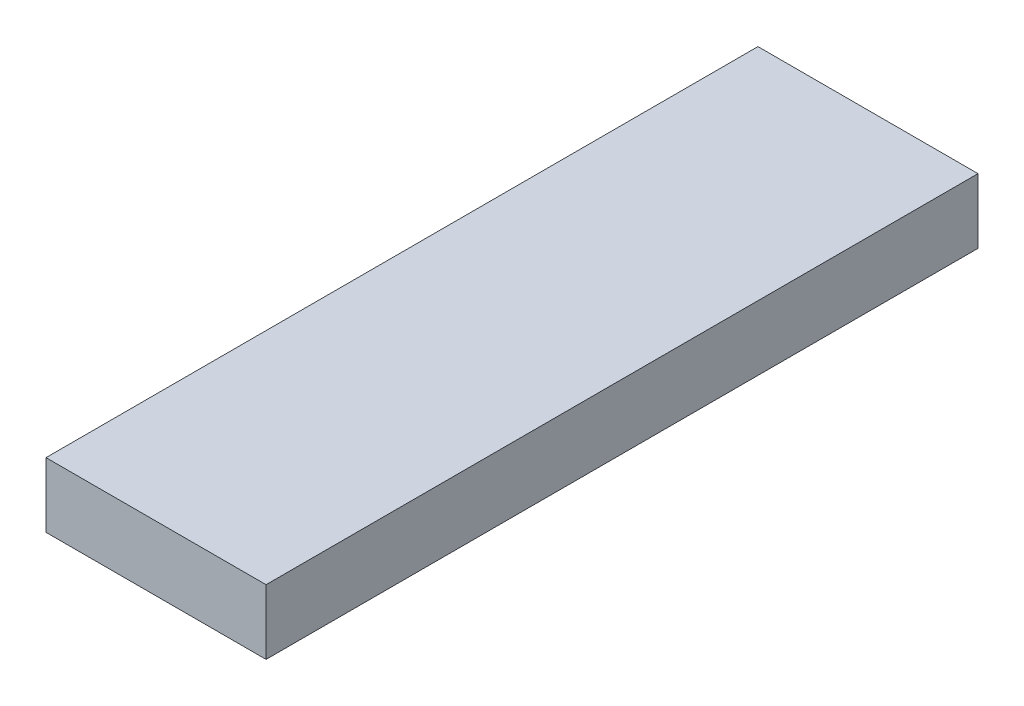
SolidWorks part; units mm, degrees
ref_plane "Front Plane" through (0, 0, 0) normal (0, 0, 1) x (1, 0, 0)
ref_plane "Top Plane" through (0, 0, 0) normal (0, 1, 0) x (1, 0, 0)
ref_plane "Right Plane" through (0, 0, 0) normal (1, 0, 0) x (0, 0, -1)
sketch "Sketch2" plane through (0, 0, 0) normal (0, 1, 0) x (1, 0, 0)
  line L1 (-4.6, 4.4326) -> (29.4, 4.4326)
  line L2 (-4.6, 4.4326) -> (-4.6, -50.5674)
  line L3 (-4.6, -50.5674) -> (29.4, -50.5674)
  line L4 (29.4, 4.4326) -> (29.4, -50.5674)
  dimension "D3" = 55
  dimension "D1" = 34
extrude "Boss-Extrude1" add sketch "Sketch2" along normal blind 10
sketch "Sketch1" plane through (0, 0, 0) normal (0, 1, 0) x (1, 0, 0)
  circle A0 centre (0, 0) radius 3.15
  circle A1 centre (24.8, 0) radius 3.15
  circle A2 centre (0, -24.8) radius 3.15
  circle A3 centre (24.8, -24.8) radius 3.15
  dimension "D1" = 6.3
  dimension "D2" = 2
  dimension "D3" = 2
extrude "Cut-Extrude1" cut sketch "Sketch1" along normal blind 5
mirror "Mirror1" about plane through (-4.6, 10, 50.5674) normal (0, 0, -1) of bodies 108
